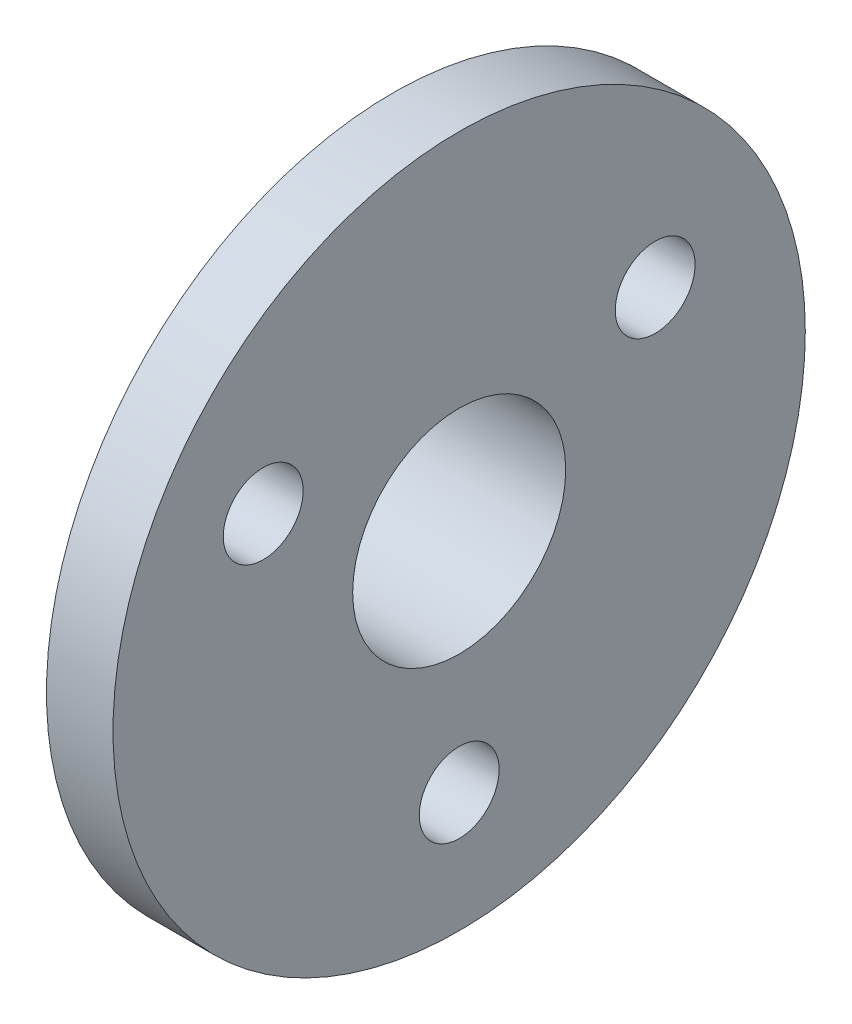
SolidWorks part; units mm, degrees
ref_plane "Front Plane" through (0, 0, 0) normal (0, 0, 1) x (1, 0, 0)
ref_plane "Top Plane" through (0, 0, 0) normal (0, 1, 0) x (1, 0, 0)
ref_plane "Right Plane" through (0, 0, 0) normal (1, 0, 0) x (0, 0, -1)
sketch "Sketch1" plane through (0, 0, 0) normal (1, 0, 0) x (0, 0, -1)
  circle A0 centre (0, 0) radius 12.5
  dimension "D1" = 25
extrude "Boss-Extrude1" add sketch "Sketch1" along normal blind 7
sketch "Sketch2" plane through (7, 0, 0) normal (1, 0, 0) x (0, 0, -1)
  circle A0 centre (0, 0) radius 26
  dimension "D1" = 52
extrude "Boss-Extrude2" add sketch "Sketch2" along normal blind 5
sketch "Sketch3" plane through (12, 0, 0) normal (1, 0, 0) x (0, 0, -1)
  circle A0 centre (0, 0) radius 8
  dimension "D1" = 16
extrude "Cut-Extrude1" cut sketch "Sketch3" against normal through all
sketch "Sketch4" plane through (12, 0, 0) normal (1, 0, 0) x (0, 0, -1)
  line L0 (0, -26) -> (0, 0) construction
  line L1 (8.8471, -17.0779) -> (8.8471, -17.0054)
  circle A0 centre (0, 0) radius 26 construction
  circle A1 centre (0, -17) radius 3
  dimension "D2" = 6
  dimension "D1" = 17
extrude "Cut-Extrude3" cut sketch "Sketch4" against normal through all contours A1 L0 | L0 A1
pattern_circular "CirPattern2" count 3 over 360 about axis through (0, 0, 0) along (1, 0, 0) of "Cut-Extrude3"
